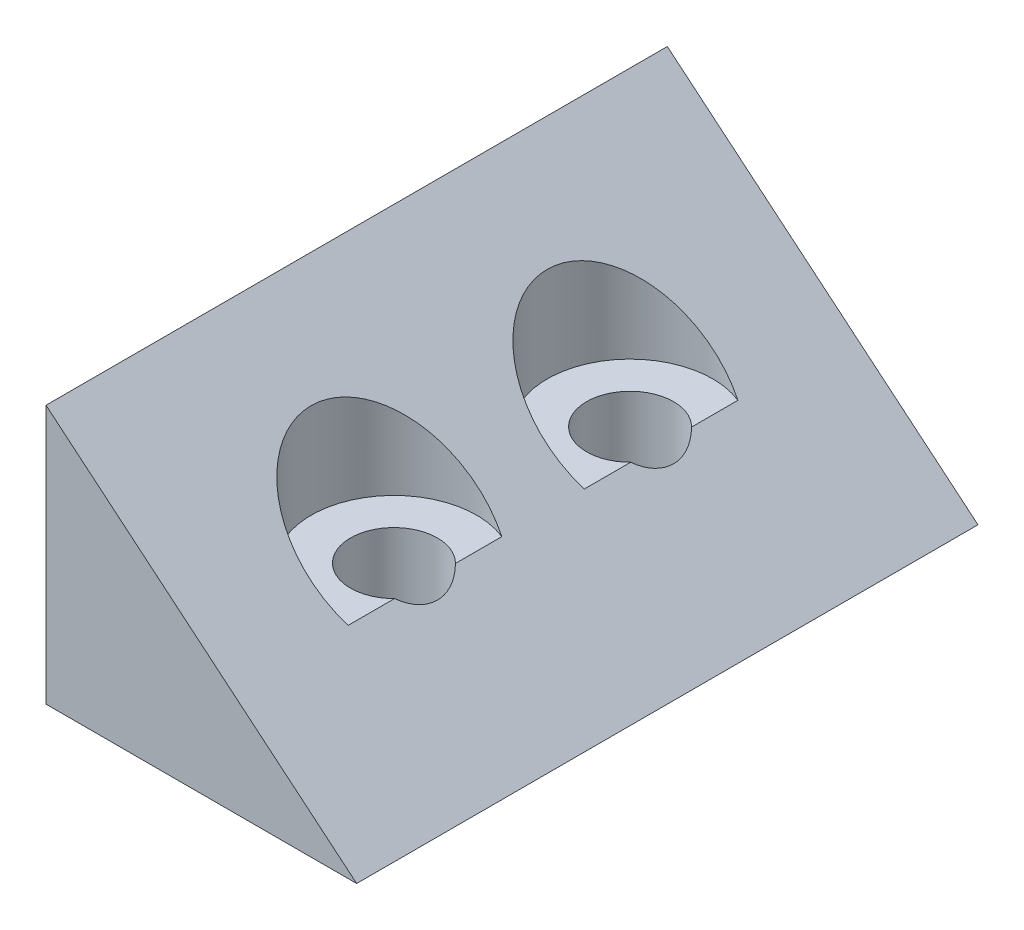
SolidWorks part; units mm, degrees
ref_plane "前基準面" through (0, 0, 0) normal (0, 0, 1) x (1, 0, 0)
ref_plane "上基準面" through (0, 0, 0) normal (0, 1, 0) x (1, 0, 0)
ref_plane "右基準面" through (0, 0, 0) normal (1, 0, 0) x (0, 0, -1)
sketch "草圖1" plane through (0, 0, 0) normal (0, 0, 1) x (1, 0, 0)
  line L0 (0, 0) -> (15, 0)
  line L1 (15, 0) -> (0, 12.5)
  line L2 (0, 12.5) -> (0, 0)
  dimension "D1" = 15
  dimension "D2" = 12.5
extrude "填料-伸長1" add sketch "草圖1" along normal blind 30
sketch "草圖2" plane through (0, 0, 0) normal (0, -1, 0) x (-1, 0, 0)
  line L0 (0, 0) -> (-15, -30)
  line L1 (-7.5, -9.3) -> (-7.5, -20.7)
  circle A0 centre (-7.5, -20.7) radius 2.1
  circle A1 centre (-7.5, -9.3) radius 2.1
  point P7 (-7.5, -15)
  dimension "D2" = 4.2
  dimension "D3" = 4.2
  dimension "D1" = 11.4
extrude "除料-伸長1" cut sketch "草圖2" against normal blind 30
sketch "草圖3" plane through (0, 0, 0) normal (0, -1, 0) x (1, 0, 0)
  circle A0 centre (7.5, 20.7) radius 4
  circle A1 centre (7.5, 9.3) radius 4
  dimension "D1" = 8
  dimension "D2" = 8
extrude "除料-伸長2" cut sketch "草圖3" against normal through all from offset 5
